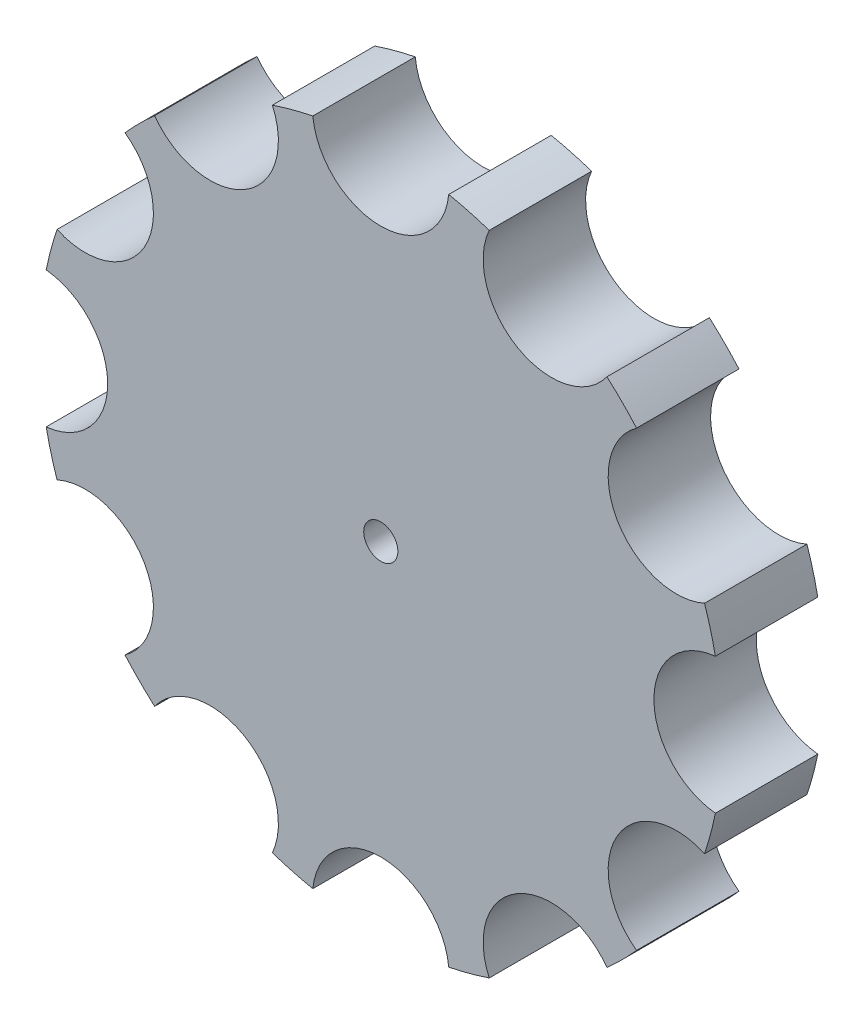
SolidWorks part; units mm, degrees
ref_plane "Front Plane" through (0, 0, 0) normal (0, 0, 1) x (1, 0, 0)
ref_plane "Top Plane" through (0, 0, 0) normal (0, 1, 0) x (1, 0, 0)
ref_plane "Right Plane" through (0, 0, 0) normal (1, 0, 0) x (0, 0, -1)
sketch "Sketch1" plane through (0, 0, 0) normal (0, 0, 1) x (1, 0, 0)
  circle A0 centre (0, 0) radius 50
  circle A11 centre (0, 0) radius 40
  circle A13 centre (0, 50) radius 10.0034
  circle A14 centre (25, 43.3013) radius 10.0034
  circle A15 centre (43.3013, 25) radius 10.0034
  circle A16 centre (50, 0) radius 10.0034
  circle A17 centre (43.3013, -25) radius 10.0034
  circle A18 centre (25, -43.3013) radius 10.0034
  circle A19 centre (0, -50) radius 10.0034
  circle A20 centre (-25, -43.3013) radius 10.0034
  circle A21 centre (-43.3013, -25) radius 10.0034
  circle A22 centre (-50, 0) radius 10.0034
  circle A23 centre (-43.3013, 25) radius 10.0034
  circle A24 centre (-25, 43.3013) radius 10.0034
  point P27 (-0.3562, -1.0707)
  point P34 (0, 0)
  dimension "D1" = 12
  dimension "D2" = 100
  dimension "D3" = 80
extrude "Boss-Extrude3" add sketch "Sketch1" along normal blind 15 contours A24 A11 A23 A22 A21 A20 A19 A18 A17 A16 A15 A14 A13 | A14 A0 A13 A11 | A15 A0 A14 A11 | A16 A0 A15 A11 | A17 A0 A16 A11 | A18 A0 A17 A11 | A19 A0 A18 A11 | A20 A0 A19 A11 | A21 A0 A20 A11 | A22 A0 A21 A11 | A23 A0 A22 A11 | A24 A0 A23 A11 | A24 A11 A13 A0
sketch "Sketch3" plane through (0, 0, 0) normal (0, 0, -1) x (-1, 0, 0)
  circle A0 centre (0, 0) radius 2.5
  dimension "D1" = 5
extrude "Cut-Extrude2" cut sketch "Sketch3" against normal blind 15
